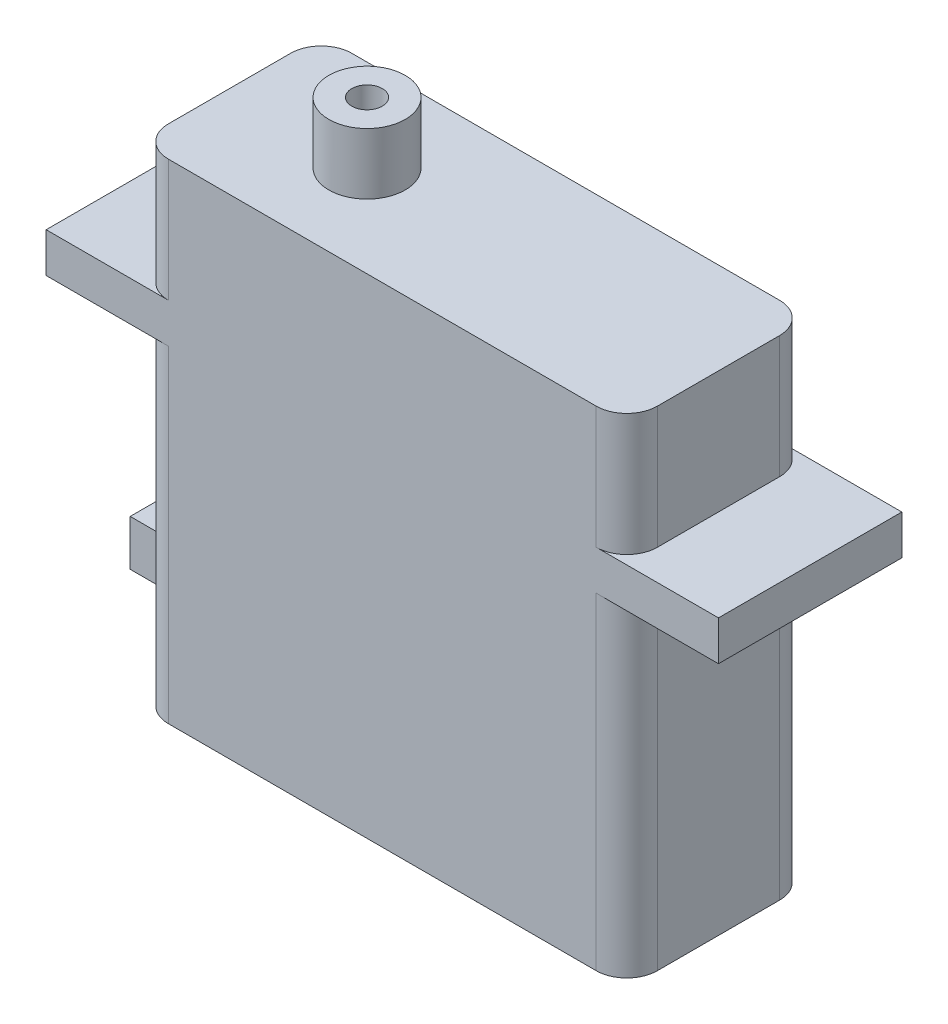
SolidWorks part; units mm, degrees
ref_plane "Front Plane" through (0, 0, 0) normal (0, 0, 1) x (1, 0, 0)
ref_plane "Top Plane" through (0, 0, 0) normal (0, 1, 0) x (1, 0, 0)
ref_plane "Right Plane" through (0, 0, 0) normal (1, 0, 0) x (0, 0, -1)
sketch "Sketch1" plane through (0, 0, 0) normal (0, 0, 1) x (1, 0, 0)
  line L1 (0.9514, 0) -> (41.5914, 0)
  line L2 (0.9514, 0) -> (0.9514, 40.64)
  line L3 (0.9514, 40.64) -> (41.5914, 40.64)
  line L4 (41.5914, 0) -> (41.5914, 40.64)
  dimension "D1" = 40.64
  dimension "D2" = 40.64
extrude "Boss-Extrude1" add sketch "Sketch1" along normal blind 15.24
sketch "Sketch2" plane through (0, 40.64, 0) normal (0, 1, 0) x (1, 0, 0)
  line L0 (41.5914, 0) -> (0.9514, 0) construction
  line L1 (0.9514, -15.24) -> (0.9514, 0) construction
  circle A0 centre (12.3814, -7.62) radius 3.175
  dimension "D1" = 6.35
  dimension "D2" = 7.62
  dimension "D3" = 11.43
extrude "Boss-Extrude2" add sketch "Sketch2" along normal blind 5.08
sketch "Sketch3" plane through (0, 45.72, 0) normal (0, 1, 0) x (1, 0, 0)
  circle A0 centre (12.3814, -7.62) radius 1.27
extrude "Cut-Extrude1" cut sketch "Sketch3" against normal blind 5.08
fillet "Fillet2" radius 2.54 4 edges at (0.9514, 20.32, 0) (0.9514, 20.32, 15.24) (41.5914, 20.32, 0) (41.5914, 20.32, 15.24)
sketch "Sketch4" plane through (0.9514, 0, 0) normal (-1, 0, 0) x (0, 0, 1)
  line L0 (12.7, 0) -> (2.54, 0) construction
  line L1 (4.445, 5.08) -> (10.795, 5.08)
  line L2 (4.445, 5.08) -> (4.445, 8.89)
  line L3 (4.445, 8.89) -> (10.795, 8.89)
  line L4 (10.795, 5.08) -> (10.795, 8.89)
  point P6 (7.62, 5.08)
  point P7 (7.62, 0)
  dimension "D1" = 5.08
  dimension "D2" = 6.35
  dimension "D3" = 3.81
extrude "Boss-Extrude3" add sketch "Sketch4" along normal blind 5.08
sketch "Sketch5" plane through (0.9514, 0, 0) normal (-1, 0, 0) x (0, 0, 1)
  line L0 (0, 0) -> (0, 40.64) construction
  line L1 (0, 30.48) -> (15.24, 30.48)
  line L2 (0, 30.48) -> (0, 27.178)
  line L3 (0, 27.178) -> (15.24, 27.178)
  line L4 (15.24, 30.48) -> (15.24, 27.178)
  line L5 (15.24, 40.64) -> (15.24, 0) construction
  line L6 (12.7, 40.64) -> (2.54, 40.64) construction
  dimension "D1" = 3.302
  dimension "D2" = 10.16
extrude "Boss-Extrude4" add sketch "Sketch5" along normal blind 7.62 and the other way blind 2.54
sketch "Sketch6" plane through (41.5914, 0, 0) normal (1, 0, 0) x (0, 0, -1)
  line L0 (-15.24, 0) -> (-15.24, 40.64) construction
  line L1 (-15.24, 30.48) -> (0, 30.48)
  line L2 (-15.24, 30.48) -> (-15.24, 27.178)
  line L3 (-15.24, 27.178) -> (0, 27.178)
  line L4 (0, 30.48) -> (0, 27.178)
  line L5 (0, 40.64) -> (0, 0) construction
  line L6 (-12.7, 40.64) -> (-2.54, 40.64) construction
  dimension "D1" = 3.302
  dimension "D2" = 10.16
extrude "Boss-Extrude5" add sketch "Sketch6" along normal blind 7.62 and the other way blind 2.54
